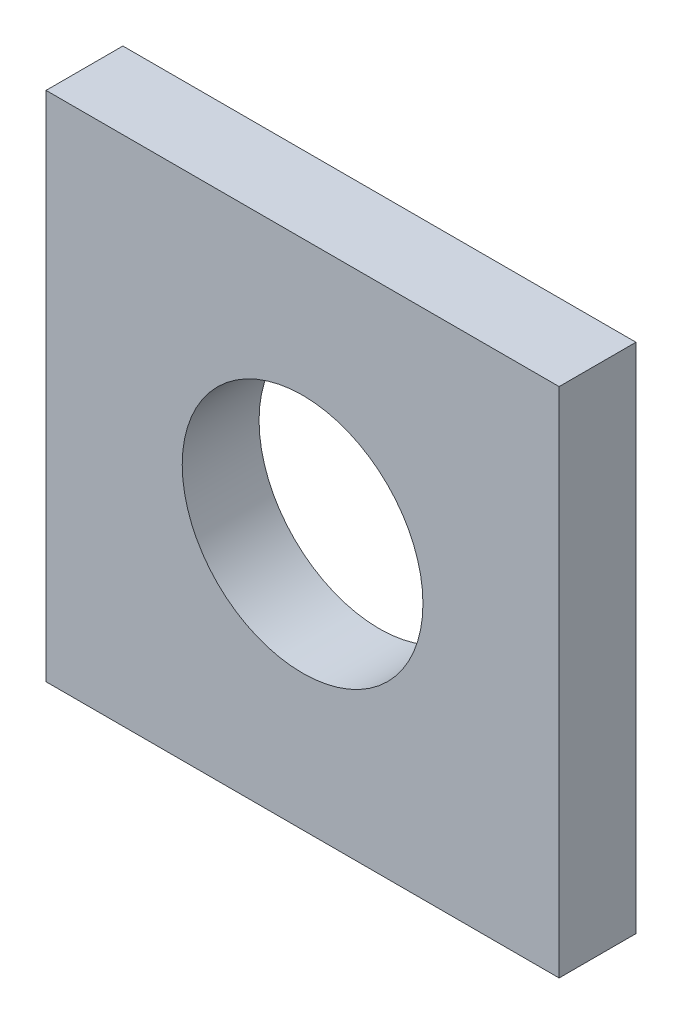
SolidWorks part; units mm, degrees
ref_plane "Plan de face" through (0, 0, 0) normal (0, 0, 1) x (1, 0, 0)
ref_plane "Plan de dessus" through (0, 0, 0) normal (0, 1, 0) x (1, 0, 0)
ref_plane "Plan de droite" through (0, 0, 0) normal (1, 0, 0) x (0, 0, -1)
sketch "Esquisse1" plane through (0, 0, 0) normal (0, 0, 1) x (1, 0, 0)
  line L0 (-76.3328, 33.8812) -> (23.8408, 33.8812)
  line L1 (-76.3328, 33.8812) -> (-76.3328, -16.1188)
  line L2 (-76.3328, -16.1188) -> (23.8408, -16.1188)
  line L3 (23.8408, 33.8812) -> (23.8408, -16.1188)
  line L5 (-76.3328, -16.1188) -> (23.8408, -16.1188)
  line L6 (-76.3328, -16.1188) -> (-76.3328, -66.1188)
  line L7 (-76.3328, -66.1188) -> (23.8408, -66.1188)
  line L8 (23.8408, -16.1188) -> (23.8408, -66.1188)
  arc A0 (-2.746, -16.1188) -> (-49.746, -16.1188) centre (-26.246, -16.1188) ccw
  circle A1 centre (-26.246, -16.1188) radius 23.5
  dimension "D1" = 23.5
  dimension "D2" = 50
extrude "Boss.-Extru.1" add sketch "Esquisse1" along normal blind 15 contours A0 L2 L3 L0 L1 | A1 L2 L6 L7 L8
